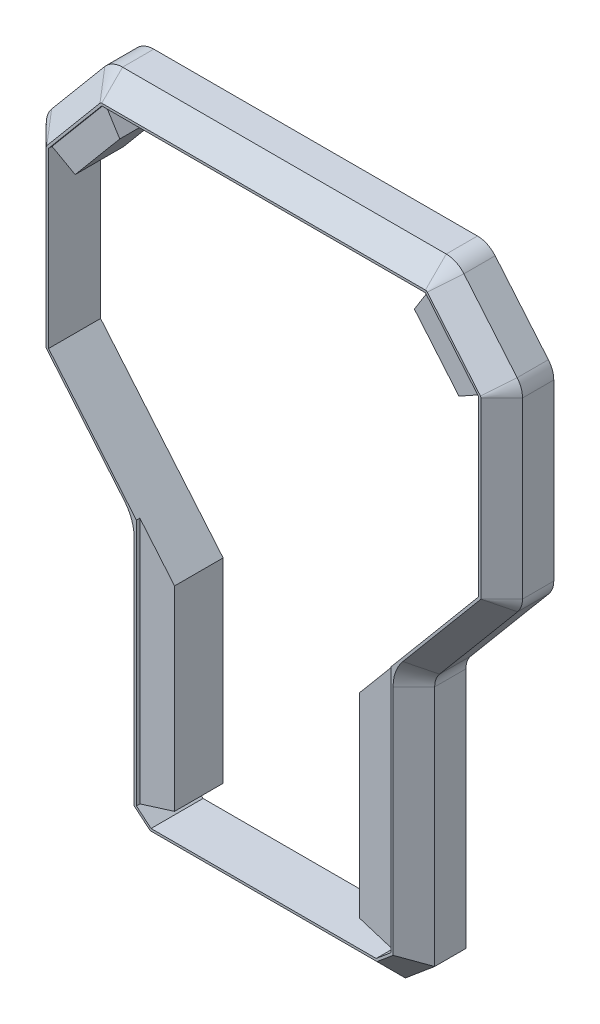
SolidWorks part; units mm, degrees
ref_plane "Plano frontal" through (0, 0, 0) normal (0, 0, 1) x (1, 0, 0)
ref_plane "Plano superior" through (0, 0, 0) normal (0, 1, 0) x (1, 0, 0)
ref_plane "Plano direito" through (0, 0, 0) normal (1, 0, 0) x (0, 0, -1)
sketch "Esboço1" plane through (0, 0, 0) normal (0, 0, 1) x (1, 0, 0)
  line L0 (-69.9918, 290.2601) -> (69.9918, 290.2601)
  line L1 (-65, 20.9002) -> (-65, 125.639)
  line L2 (-67.1215, 131.4677) -> (-100.8785, 171.6978)
  line L3 (-103, 177.5265) -> (-103, 252.84)
  line L4 (-63.7057, 270.2601) -> (63.7057, 270.2601)
  line L5 (0, 290.2601) -> (0, 0) construction
  line L6 (-77.6523, 286.6879) -> (-100.6604, 259.2679)
  line L7 (-83, 181.5055) -> (-83, 247.266)
  line L8 (-83, 247.266) -> (-63.7057, 270.2601)
  line L9 (-40, 30.2601) -> (40, 30.2601)
  line L10 (-40, 30.2601) -> (-40, 130.2601)
  line L11 (-40, 130.2601) -> (-83, 181.5055)
  line L12 (-65, 20.9002) -> (-52.3196, 10.2601)
  line L13 (-52.3196, 10.2601) -> (52.3196, 10.2601)
  line L14 (65, 20.9002) -> (52.3196, 10.2601)
  line L15 (40, 130.2601) -> (83, 181.5055)
  line L16 (40, 30.2601) -> (40, 130.2601)
  line L17 (83, 247.266) -> (63.7057, 270.2601)
  line L18 (83, 181.5055) -> (83, 247.266)
  line L19 (77.6523, 286.6879) -> (100.6604, 259.2679)
  line L20 (103, 177.5265) -> (103, 252.84)
  line L21 (67.1215, 131.4677) -> (100.8785, 171.6978)
  line L22 (65, 20.9002) -> (65, 125.639)
  arc A0 (-103, 252.84) -> (-100.6604, 259.2679) centre (-93, 252.84) cw
  arc A1 (-100.8785, 171.6978) -> (-103, 177.5265) centre (-93.9321, 177.5265) cw
  arc A2 (-65, 125.639) -> (-67.1215, 131.4677) centre (-74.0679, 125.639) ccw
  arc A3 (69.9918, 290.2601) -> (77.6523, 286.6879) centre (69.9918, 280.2601) cw
  arc A4 (-69.9918, 290.2601) -> (-77.6523, 286.6879) centre (-69.9918, 280.2601) ccw
  arc A5 (65, 125.639) -> (67.1215, 131.4677) centre (74.0679, 125.639) cw
  arc A6 (100.8785, 171.6978) -> (103, 177.5265) centre (93.9321, 177.5265) ccw
  arc A7 (103, 252.84) -> (100.6604, 259.2679) centre (93, 252.84) ccw
  point P27 (-103, 256.4797)
  point P33 (0, 30.2601)
  point P35 (0, 10.2601)
  point P40 (0, 270.2601)
  point P45 (0, 30.2601)
  point P46 (0, 30.2601)
  point P48 (0, 270.2601)
  point P53 (0, 280)
  dimension "D7" = 40
  dimension "D12" = 10
  dimension "D14" = 10
  dimension "D16" = 20
  dimension "D5" = 40
  dimension "D2" = 103
  dimension "D3" = 20
  dimension "D4" = 65
  dimension "D6" = 40
  dimension "D8" = 20
  dimension "D9" = 280
  dimension "D10" = 25
  dimension "D11" = 100
  dimension "D13" = 40
  dimension "D15" = 20
extrude "Ressalto-extrusão1" add sketch "Esboço1" along normal mid plane 45
chamfer "Chanfro1" distance 9 angle 45 20 edges at (0, 10.2601, 22.5) (-65, 73.2696, 22.5) (-65.5469, 128.7404, 22.5) (-84, 151.5827, 22.5) (0, 290.2601, 22.5) (-102.4531, 174.4251, 22.5) (-89.1564, 272.9779, 22.5) (-103, 215.1833, 22.5) (65.5469, 128.7404, 22.5) (74.218, 289.3231, 22.5) (-74.218, 289.3231, 22.5) (-102.3969, 256.2602, 22.5) (-58.6598, 15.5801, 22.5) (89.1564, 272.9779, 22.5) (102.3969, 256.2602, 22.5) (103, 215.1833, 22.5) (102.4531, 174.4251, 22.5) (84, 151.5827, 22.5) (65, 73.2696, 22.5) (58.6598, 15.5801, 22.5)
sketch "Esboço3" plane through (0, 0, 0) normal (0, 0, 1) x (1, 0, 0)
  line L1 (-722.7729, 507.4347) -> (416.458, 507.4347)
  line L2 (-722.7729, 507.4347) -> (-722.7729, -202.3634)
  line L3 (-722.7729, -202.3634) -> (416.458, -202.3634)
  line L4 (416.458, 507.4347) -> (416.458, -202.3634)
extrude "Corte-extrusão1" cut sketch "Esboço3" against normal up to next
sketch "Esboço4" plane through (0, 0, 22.5) normal (0, 0, 1) x (1, 0, 0)
  line L0 (40, 30.2601) -> (-40, 30.2601)
  line L1 (-40, 30.2601) -> (40, 30.2601) construction
  line L3 (-40, 30.2601) -> (-40, 130.2601)
  line L4 (-40, 30.2601) -> (-40, 130.2601) construction
  line L5 (0, -6.7811) -> (0, 343.2781) construction
  line L6 (-40, 130.2601) -> (-83, 181.5055)
  line L8 (-83, 181.5055) -> (-83, 247.266)
  line L9 (-83, 247.266) -> (-63.7057, 270.2601)
  line L11 (-63.7057, 270.2601) -> (63.7057, 270.2601)
  line L12 (-63.7057, 270.2601) -> (63.7057, 270.2601) construction
  line L13 (69.9918, 280.2601) -> (-69.9918, 280.2601)
  line L14 (-69.9918, 280.2601) -> (-93, 252.84)
  line L15 (-93, 252.84) -> (-93, 177.8658)
  line L16 (-93, 177.8658) -> (-55, 132.5791)
  line L18 (-55, 132.5791) -> (-55, 25.5633)
  line L19 (-55, 25.5633) -> (-48.6799, 20.2601)
  line L20 (-48.6799, 20.2601) -> (48.6799, 20.2601)
  line L21 (69.9918, 281.2601) -> (-69.9918, 281.2601) construction
  line L22 (-70.7579, 280.9028) -> (-93.766, 253.4828) construction
  line L24 (-94, 252.84) -> (-94, 177.5265) construction
  line L25 (-56, 125.639) -> (-56, 25.097) construction
  line L26 (-49.0438, 19.2601) -> (49.0438, 19.2601) construction
  line L27 (-93.9841, 177.4829) -> (-60.2271, 137.2528) construction
  line L32 (-56, 25.097) -> (-49.0438, 19.2601) construction
  line L33 (55, 25.5633) -> (48.6799, 20.2601)
  line L34 (55, 132.5791) -> (55, 25.5633)
  line L35 (93, 177.8658) -> (55, 132.5791)
  line L36 (93, 252.84) -> (93, 177.8658)
  line L37 (69.9918, 280.2601) -> (93, 252.84)
  line L38 (83, 247.266) -> (63.7057, 270.2601)
  line L39 (83, 181.5055) -> (83, 247.266)
  line L40 (40, 130.2601) -> (83, 181.5055)
  line L41 (40, 30.2601) -> (40, 130.2601)
  point P40 (0, 20.2601)
  point P44 (0, 280.2601)
  point P45 (0, 270.2601)
  point P46 (0, 30.2601)
  dimension "D1" = 1
  dimension "D2" = 1
  dimension "D3" = 1
  dimension "D4" = 1
  dimension "D5" = 1
  dimension "D6" = 1
  dimension "D7" = 1
extrude "Corte-extrusão5" cut sketch "Esboço4" against normal blind 1.5
sketch "Esboço5" plane through (0, 0, 21) normal (0, 0, 1) x (1, 0, 0)
  line L0 (-93, 252.84) -> (-83, 247.266)
  line L1 (-83, 247.266) -> (-83, 181.5055)
  line L2 (-83, 181.5055) -> (-40, 130.2601)
  line L3 (-93, 177.8658) -> (-93, 252.84)
  line L4 (-40, 130.2601) -> (-40, 30.2601) construction
  line L5 (-40, 114.7028) -> (-93, 177.8658)
  line L6 (0, -17.6729) -> (0, 329.9726) construction
  line L7 (-63.7057, 270.2601) -> (-69.9918, 280.2601)
  line L8 (-69.9918, 280.2601) -> (69.9918, 280.2601)
  line L9 (69.9918, 280.2601) -> (-69.9918, 280.2601) construction
  line L10 (-63.7057, 270.2601) -> (63.7057, 270.2601)
  line L11 (63.7057, 270.2601) -> (-63.7057, 270.2601) construction
  line L12 (-55, 25.5633) -> (-40, 30.2601)
  line L13 (-40, 30.2601) -> (40, 30.2601)
  line L14 (40, 30.2601) -> (-40, 30.2601) construction
  line L15 (-55, 25.5633) -> (-48.6799, 20.2601)
  line L16 (-48.6799, 20.2601) -> (48.6799, 20.2601)
  line L17 (-48.6799, 20.2601) -> (48.6799, 20.2601) construction
  line L18 (55, 25.5633) -> (48.6799, 20.2601)
  line L19 (55, 25.5633) -> (40, 30.2601)
  line L20 (63.7057, 270.2601) -> (69.9918, 280.2601)
  line L21 (40, 114.7028) -> (93, 177.8658)
  line L22 (40, 130.2601) -> (40, 114.7028)
  line L23 (93, 177.8658) -> (93, 252.84)
  line L24 (83, 181.5055) -> (40, 130.2601)
  line L25 (83, 247.266) -> (83, 181.5055)
  line L26 (93, 252.84) -> (83, 247.266)
  line L29 (-93, 177.8658) -> (-55, 132.5791) construction
  line L30 (-40, 114.7028) -> (-40, 130.2601)
  point P38 (0, 20.2601)
  point P40 (0, 30.2601)
  point P41 (0, 270.2601)
  point P42 (0, 280.2601)
extrude "Corte-extrusão6" cut sketch "Esboço5" against normal up to next
